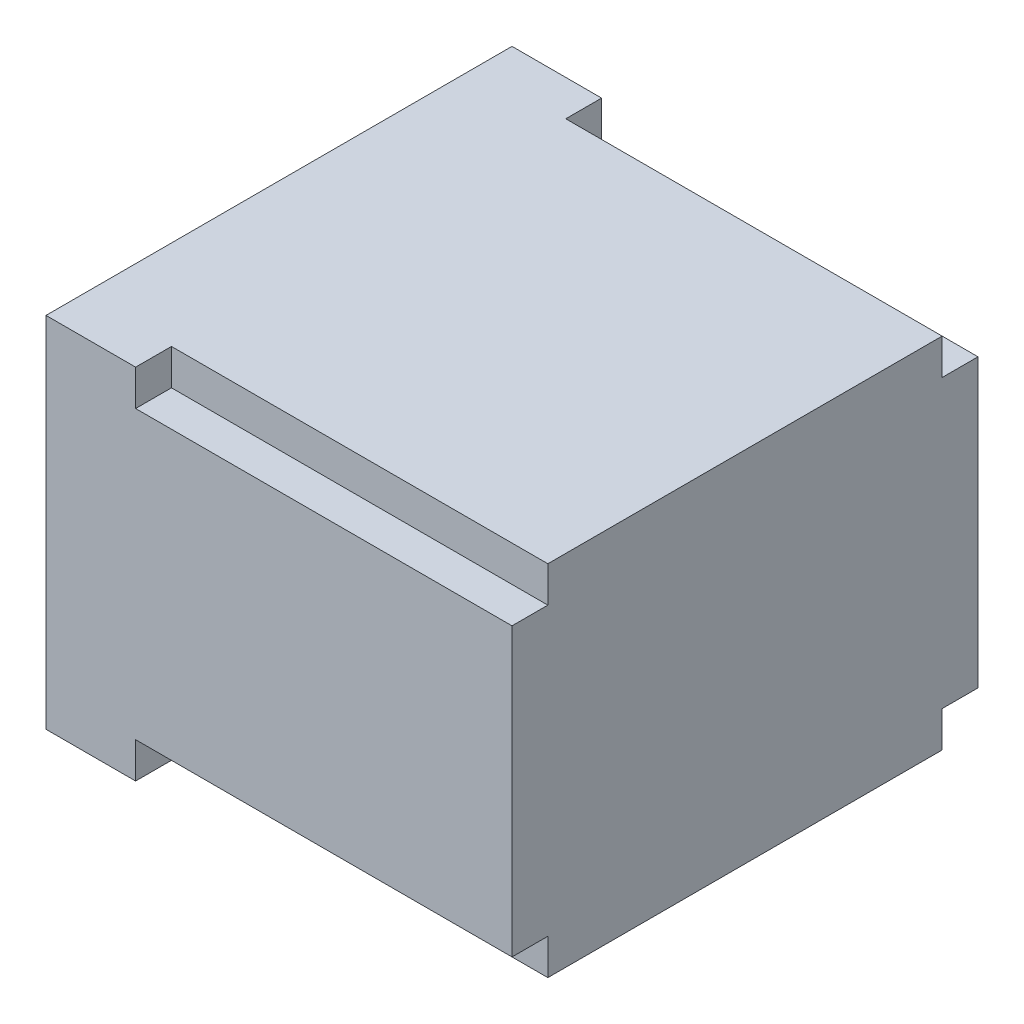
SolidWorks part; units mm, degrees
ref_plane "Front Plane" through (0, 0, 0) normal (0, 0, 1) x (1, 0, 0)
ref_plane "Top Plane" through (0, 0, 0) normal (0, 1, 0) x (1, 0, 0)
ref_plane "Right Plane" through (0, 0, 0) normal (1, 0, 0) x (0, 0, -1)
sketch "Sketch2" plane through (0, 0, 0) normal (0, 1, 0) x (1, 0, 0)
  line L1 (0, 0) -> (130, 0)
  line L2 (0, 0) -> (0, 130)
  line L3 (0, 130) -> (130, 130)
  line L4 (130, 0) -> (130, 130)
  dimension "D1" = 130
  dimension "D2" = 130
extrude "Boss-Extrude1" add sketch "Sketch2" along normal blind 100
sketch "Sketch3" plane through (0, 0, 0) normal (-1, 0, 0) x (0, 0, 1)
  line L0 (-130, 100) -> (0, 100) construction
  line L1 (-117, 13) -> (-13, 13)
  line L2 (-117, 13) -> (-117, 87)
  line L3 (-117, 87) -> (-13, 87)
  line L4 (-13, 13) -> (-13, 87)
  line L5 (0, 100) -> (0, 0) construction
  line L6 (-130, 0) -> (0, 0) construction
  line L7 (-130, 100) -> (-130, 0) construction
  dimension "D1" = 13
  dimension "D2" = 13
  dimension "D3" = 13
  dimension "D4" = 13
extrude "Cut-Extrude1" cut sketch "Sketch3" against normal blind 127
sketch "Sketch4" plane through (130, 0, 0) normal (1, 0, 0) x (0, 0, -1)
  line L1 (0, 100) -> (10, 100)
  line L2 (0, 100) -> (0, 90)
  line L3 (0, 90) -> (10, 90)
  line L4 (10, 100) -> (10, 90)
  line L5 (130, 100) -> (120, 100)
  line L6 (130, 100) -> (130, 90)
  line L7 (130, 90) -> (120, 90)
  line L8 (120, 100) -> (120, 90)
  line L9 (0, 0) -> (10, 0)
  line L10 (0, 0) -> (0, 10)
  line L11 (0, 10) -> (10, 10)
  line L12 (10, 0) -> (10, 10)
  line L13 (130, 0) -> (120, 0)
  line L14 (130, 0) -> (130, 10)
  line L15 (130, 10) -> (120, 10)
  line L16 (120, 0) -> (120, 10)
  dimension "D1" = 10
  dimension "D2" = 10
  dimension "D3" = 10
  dimension "D4" = 10
  dimension "D5" = 10
  dimension "D6" = 10
  dimension "D7" = 10
  dimension "D8" = 10
extrude "Cut-Extrude3" cut sketch "Sketch4" against normal blind 105
sketch "Sketch5" plane through (0, 0, 0) normal (-1, 0, 0) x (0, 0, 1)
  line L0 (-130, 100) -> (0, 100) construction
  line L1 (-117, 87) -> (-13, 87)
  line L2 (-117, 87) -> (-117, 97)
  line L3 (-117, 97) -> (-13, 97)
  line L4 (-13, 87) -> (-13, 97)
  line L5 (-117, 13) -> (-13, 13)
  line L6 (-117, 13) -> (-117, 3)
  line L7 (-117, 3) -> (-13, 3)
  line L8 (-13, 13) -> (-13, 3)
  line L9 (-130, 0) -> (0, 0) construction
  line L10 (0, 100) -> (0, 0) construction
  dimension "D1" = 3
  dimension "D2" = 3
  dimension "D3" = 13
  dimension "D4" = 13
extrude "Cut-Extrude4" cut sketch "Sketch5" against normal blind 127
sketch "Sketch6" plane through (0, 0, 0) normal (-1, 0, 0) x (0, 0, 1)
  line L0 (-117, 97) -> (-117, 3) construction
  line L1 (-117, 87) -> (-127, 87)
  line L2 (-117, 87) -> (-117, 13)
  line L3 (-117, 13) -> (-127, 13)
  line L4 (-127, 87) -> (-127, 13)
  line L5 (-13, 3) -> (-13, 97) construction
  line L6 (-13, 87) -> (-3, 87)
  line L7 (-13, 87) -> (-13, 13)
  line L8 (-13, 13) -> (-3, 13)
  line L9 (-3, 87) -> (-3, 13)
  line L10 (-130, 100) -> (-130, 0) construction
  line L11 (0, 100) -> (0, 0) construction
  line L12 (-130, 100) -> (0, 100) construction
  line L13 (-130, 0) -> (0, 0) construction
  dimension "D1" = 3
  dimension "D2" = 3
  dimension "D3" = 13
  dimension "D4" = 13
  dimension "D5" = 13
  dimension "D6" = 13
extrude "Cut-Extrude5" cut sketch "Sketch6" against normal blind 127
sketch "Sketch7" plane through (0, 0, 0) normal (-1, 0, 0) x (0, 0, 1)
  line L0 (0, 100) -> (0, 0) construction
  line L1 (-130, 0) -> (0, 0) construction
  line L2 (-130, 100) -> (-130, 0) construction
  line L3 (-130, 100) -> (0, 100) construction
  circle A0 centre (-124, 94) radius 1.75
  circle A1 centre (-6, 94) radius 1.75
  circle A2 centre (-124, 6) radius 1.75
  circle A3 centre (-6, 6) radius 1.75
  point P8 (-6.524, 6.1927)
  dimension "D3" = 3.5
  dimension "D6" = 3.5
  dimension "D9" = 3.5
  dimension "D12" = 3.5
  dimension "D1" = 6
  dimension "D2" = 6
  dimension "D4" = 6
  dimension "D5" = 6
  dimension "D7" = 6
  dimension "D8" = 6
  dimension "D10" = 6
  dimension "D11" = 6
extrude "Cut-Extrude6" cut sketch "Sketch7" against normal blind 20
sketch "Sketch8" plane through (0, 0, 0) normal (-1, 0, 0) x (0, 0, 1)
  line L1 (-117, 87) -> (-120, 87)
  line L2 (-117, 87) -> (-117, 90)
  line L3 (-117, 90) -> (-120, 90)
  line L4 (-120, 87) -> (-120, 90)
  line L5 (-13, 87) -> (-10, 87)
  line L6 (-13, 87) -> (-13, 90)
  line L7 (-13, 90) -> (-10, 90)
  line L8 (-10, 87) -> (-10, 90)
  line L9 (-117, 13) -> (-120, 13)
  line L10 (-117, 13) -> (-117, 10)
  line L11 (-117, 10) -> (-120, 10)
  line L12 (-120, 13) -> (-120, 10)
  line L13 (-13, 13) -> (-10, 13)
  line L14 (-13, 13) -> (-13, 10)
  line L15 (-13, 10) -> (-10, 10)
  line L16 (-10, 13) -> (-10, 10)
  dimension "D1" = 3
  dimension "D2" = 3
  dimension "D3" = 3
  dimension "D4" = 3
  dimension "D5" = 3
  dimension "D6" = 3
  dimension "D7" = 3
  dimension "D8" = 3
extrude "Cut-Extrude7" cut sketch "Sketch8" against normal blind 5
